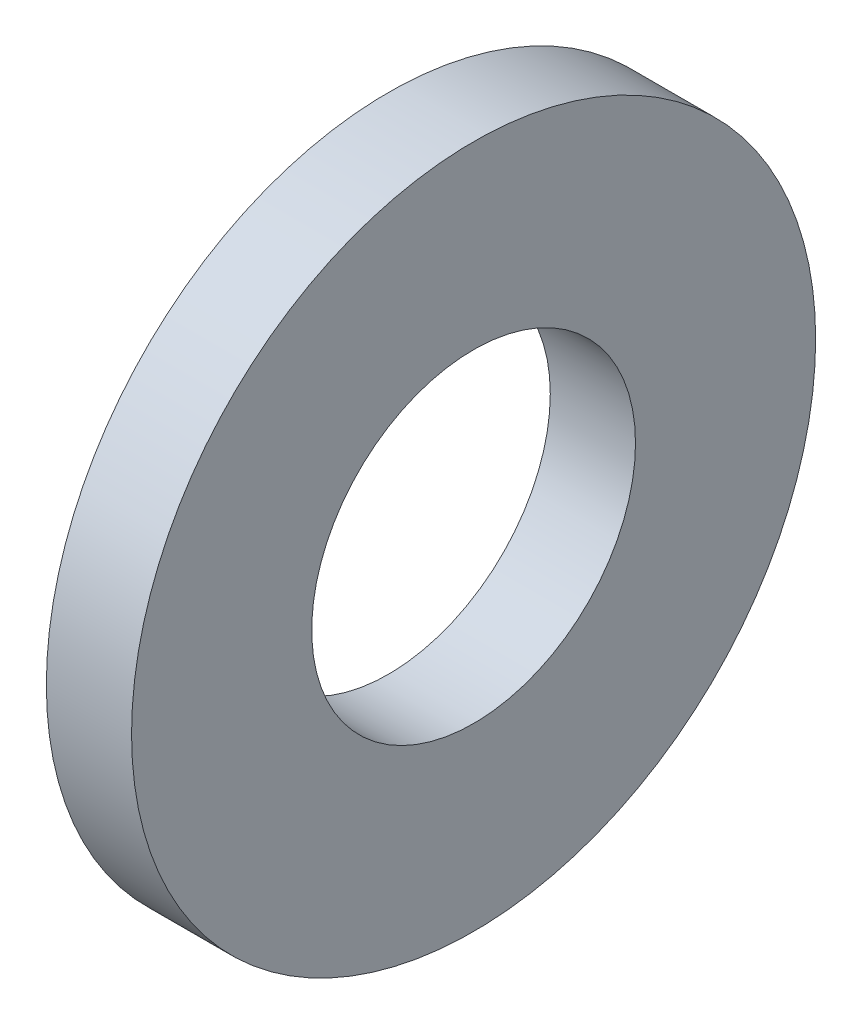
SolidWorks part; units mm, degrees
material "AISI Type 316L stainless steel"
ref_plane "Front Plane" through (0, 0, 0) normal (0, 0, 1) x (1, 0, 0)
ref_plane "Top Plane" through (0, 0, 0) normal (0, 1, 0) x (1, 0, 0)
ref_plane "Right Plane" through (0, 0, 0) normal (1, 0, 0) x (0, 0, -1)
sketch "Sketch1" plane through (0, 0, 0) normal (1, 0, 0) x (0, 0, -1)
  circle A0 centre (0, 0) radius 7.1374
  circle A1 centre (0, 0) radius 3.3782
  dimension "OD" = 14.2748
  dimension "ID" = 6.7564
extrude "Boss-Extrude1" add sketch "Sketch1" along normal blind 1.778
